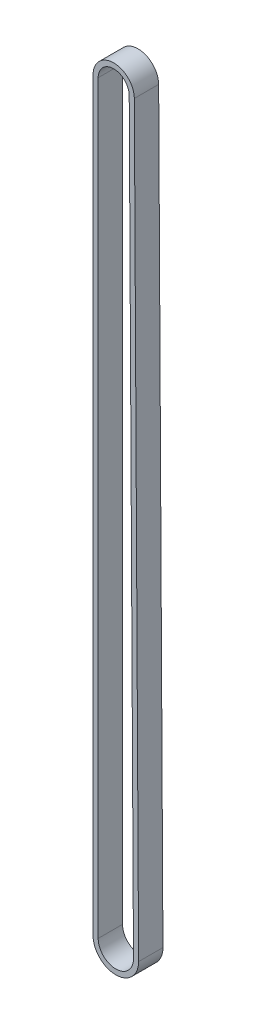
SolidWorks part; units mm, degrees
material "VITON"
ref_plane "Front Plane" through (0, 0, 0) normal (0, 0, 1) x (1, 0, 0)
ref_plane "Top Plane" through (0, 0, 0) normal (0, 1, 0) x (1, 0, 0)
ref_plane "Right Plane" through (0, 0, 0) normal (1, 0, 0) x (0, 0, -1)
sketch "Sketch1" plane through (0, 0, 0) normal (0, 0, 1) x (1, 0, 0)
  line L1 (342.2664, -304.1459) -> (341.2789, -132.1724) construction
  line L2 (324.7565, -302.4459) -> (324.7561, -112.5526)
  line L3 (336.3564, -302.4126) -> (335.266, -112.5224)
  line L4 (326.0565, -302.4459) -> (326.0561, -112.5526)
  line L6 (335.0564, -302.4201) -> (333.966, -112.5299)
  line L7 (355.1735, -96.3579) -> (356.4251, -314.3298) construction
  arc A0 (336.3564, -302.4126) -> (324.7565, -302.4459) centre (330.5565, -302.4459) cw
  arc A1 (335.266, -112.5224) -> (324.7561, -112.5526) centre (330.0111, -112.5526) ccw
  circle A2 centre (330.0111, -112.5526) radius 3.955 construction
  arc A7 (333.966, -112.5299) -> (326.0561, -112.5526) centre (330.0111, -112.5526) ccw
  arc A9 (335.0564, -302.4201) -> (326.0565, -302.4459) centre (330.5565, -302.4459) cw
  point P7 (34.3966, -33.749)
  point P28 (35.5953, -32.4056)
  dimension "D3" = 4.5
  dimension "D6" = 1.3
  dimension "D2" = 1.3
extrude "Boss-Extrude1" add sketch "Sketch1" against normal blind 6.2
